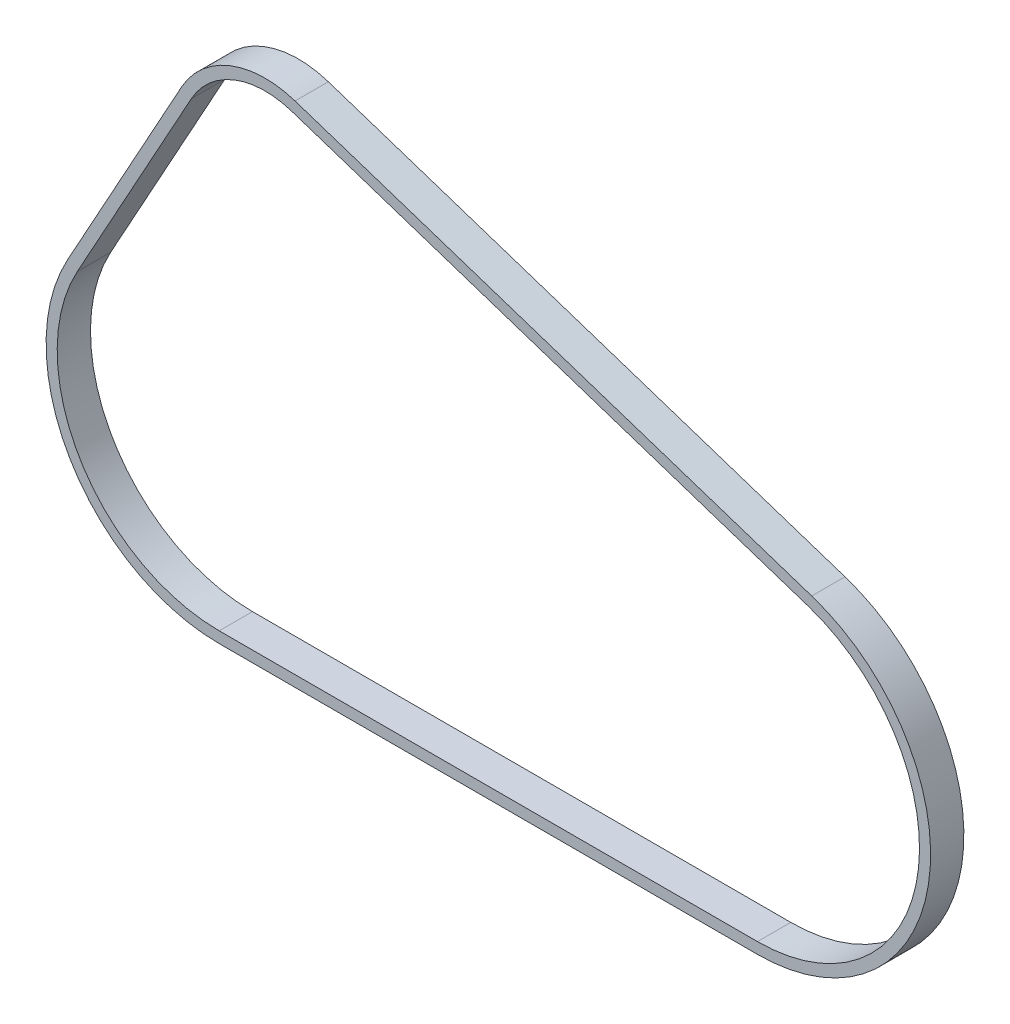
SolidWorks part; units mm, degrees
ref_plane "Front Plane" through (0, 0, 0) normal (0, 0, 1) x (1, 0, 0)
ref_plane "Top Plane" through (0, 0, 0) normal (0, 1, 0) x (1, 0, 0)
ref_plane "Right Plane" through (0, 0, 0) normal (1, 0, 0) x (0, 0, -1)
sketch "Sketch2" plane through (0, 0, 0) normal (0, 0, 1) x (1, 0, 0)
  line L0 (0, 0) -> (1, 0) construction
  line L1 (0, 0) -> (0, 1) construction
  line L2 (-33.2721, 18.3567) -> (-84.6326, -74.7358)
  line L3 (-20.7151, -183) -> (221.8191, -183)
  line L4 (244.6804, -40.6721) -> (11.9004, 36.0885)
  arc A0 (11.9004, 36.0885) -> (-33.2721, 18.3567) centre (0, 0) ccw
  arc A1 (-84.6326, -74.7358) -> (-20.7151, -183) centre (-20.7151, -110) ccw
  arc A2 (221.8191, -183) -> (244.6804, -40.6721) centre (221.8191, -110) ccw
extrude "Extrude-Thin1" add sketch "Sketch2" along normal blind 7.5 and the other way blind 7.5 thin
